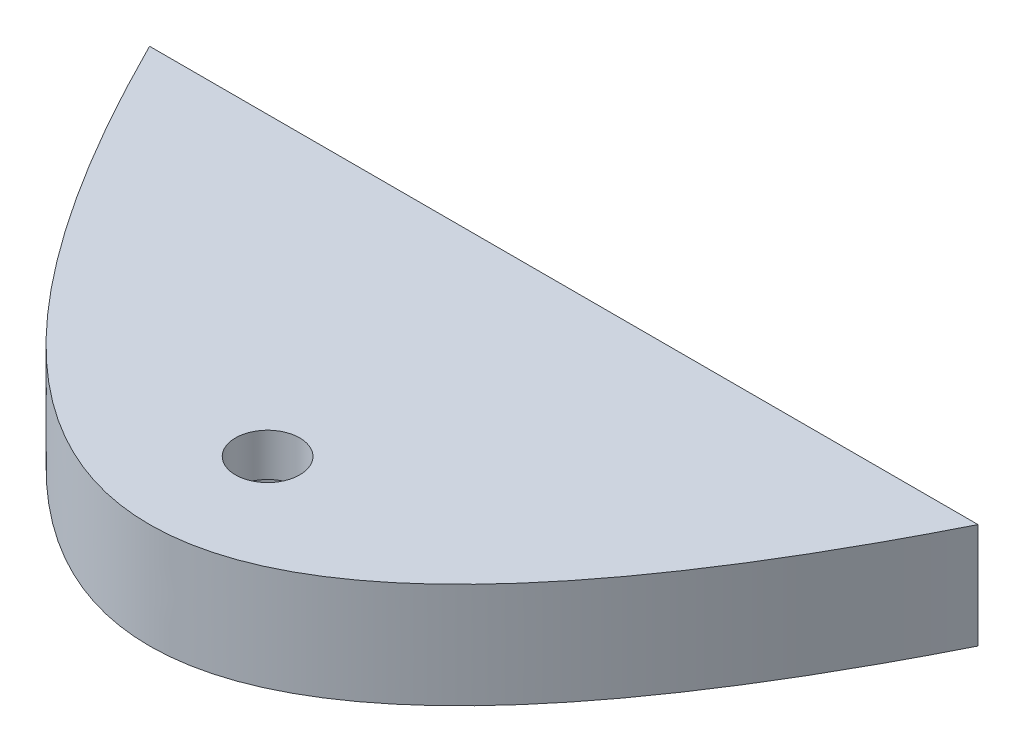
SolidWorks part; units mm, degrees
material "Custom Plastic (2)"
ref_plane "Front Plane" through (0, 0, 0) normal (0, 0, 1) x (1, 0, 0)
ref_plane "Top Plane" through (0, 0, 0) normal (0, 1, 0) x (1, 0, 0)
ref_plane "Right Plane" through (0, 0, 0) normal (1, 0, 0) x (0, 0, -1)
sketch "Sketch1" plane through (0, 0, 0) normal (0, 1, 0) x (1, 0, 0)
  line L0 (-200, 0) -> (200, 0)
  spline S0 degree 2 poles (-225.2396, 53.6645) (0, -453.6645) (225.2396, 53.6645) knots 0 0 0 1 1 1 construction
  spline S1 degree 2 poles (-200, 0) (0, -400) (200, 0) knots 0.056028 0.056028 0.056028 0.943972 0.943972 0.943972
extrude "Boss-Extrude1" add sketch "Sketch1" along normal blind 300
sketch "Sketch2" plane through (0, 300, 0) normal (0, 1, 0) x (1, 0, 0)
  line L0 (0, 200) -> (0, -200)
  line L2 (200, 0) -> (-200, 0) construction
  circle A0 centre (0, -143) radius 35
  parabola Q0 (-200, 0) -> (200, 0) focus (0, -150) apex (0, -200) construction
  point P4 (0, 0)
  dimension "D1" = 70
  dimension "D2" = 143
ref_plane "Plane1" through (0, 150, 0) normal (0, 1, 0) x (1, 0, 0)
sketch "Sketch3" plane through (0, 150, 0) normal (0, 1, 0) x (1, 0, 0)
  circle A0 centre (0, -143) radius 15.5
  dimension "D1" = 31
extrude "Cut-Extrude1" cut sketch "Sketch3" against normal blind 23 and the other way blind 23
ref_plane "Plane2" through (0, 173, 0) normal (0, 1, 0) x (1, 0, 0)
sketch "Sketch4" plane through (0, 173, 0) normal (0, 1, 0) x (1, 0, 0)
  circle A0 centre (0, -143) radius 35
extrude "Cut-Extrude3" cut sketch "Sketch4" along normal blind 300 contours A0
mirror "Mirror1" about plane through (0, 150, 0) normal (0, 1, 0) of "Cut-Extrude3"
sketch "Sketch5" plane through (0, 0, 0) normal (0, 0, -1) x (-1, 0, 0)
  line L0 (-200, 300) -> (200, 300) construction
  line L1 (-245.4318, 376.2148) -> (243.482, 376.2148)
  line L2 (-245.4318, 376.2148) -> (-245.4318, 147.6)
  line L3 (-245.4318, 147.6) -> (243.482, 147.6)
  line L4 (243.482, 376.2148) -> (243.482, 147.6)
  line L6 (-245.4318, 96.8) -> (251.2813, 96.8)
  line L7 (-245.4318, 96.8) -> (-245.4318, -10.9268)
  line L8 (-245.4318, -10.9268) -> (251.2813, -10.9268)
  line L9 (251.2813, 96.8) -> (251.2813, -10.9268)
  dimension "D1" = 152.4
  dimension "D2" = 203.2
extrude "Cut-Extrude4" cut sketch "Sketch5" against normal through all
